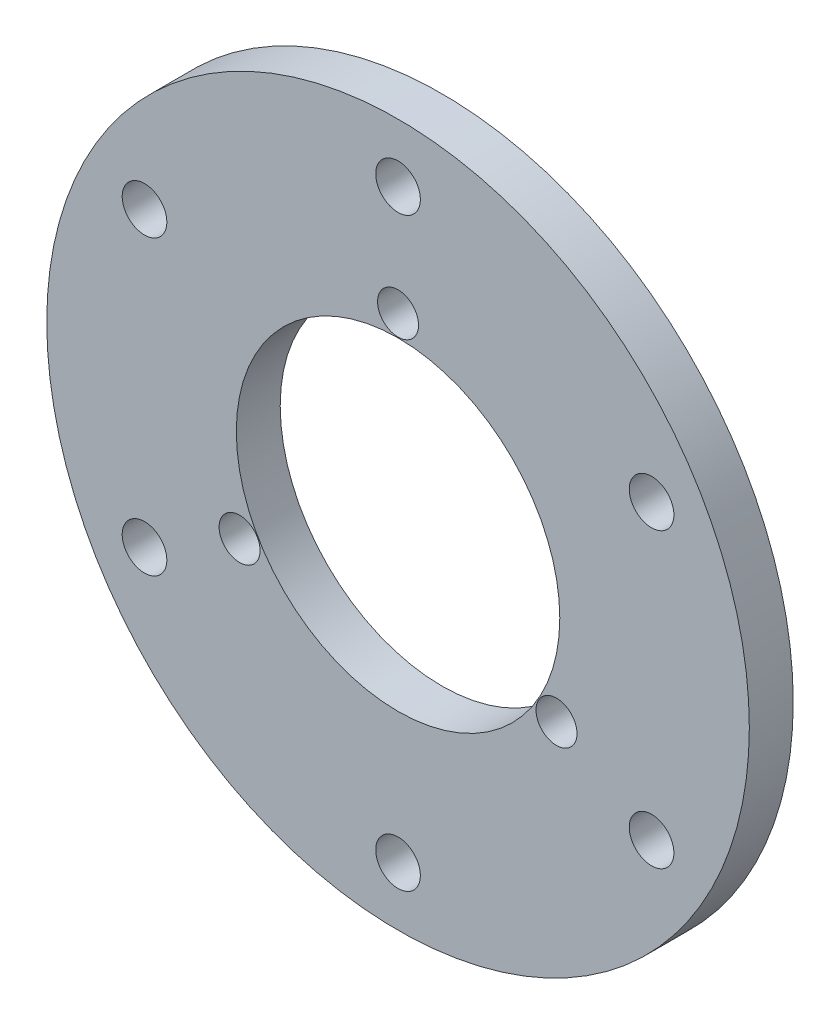
SolidWorks part; units mm, degrees
material "Thornel Mat VMA"
ref_plane "前视基准面" through (0, 0, 0) normal (0, 0, 1) x (1, 0, 0)
ref_plane "上视基准面" through (0, 0, 0) normal (0, 1, 0) x (1, 0, 0)
ref_plane "右视基准面" through (0, 0, 0) normal (1, 0, 0) x (0, 0, -1)
sketch "草图1" plane through (0, 0, 0) normal (0, 0, 1) x (1, 0, 0)
  circle A0 centre (0, 0) radius 11.05
  circle A1 centre (0, 0) radius 12.5 construction
  circle A2 centre (0, 0) radius 20 construction
  circle A3 centre (0, 0) radius 24
  circle A4 centre (0, 20) radius 1.525
  circle A5 centre (17.3205, 10) radius 1.525
  circle A6 centre (17.3205, -10) radius 1.525
  circle A7 centre (0, -20) radius 1.525
  circle A8 centre (-17.3205, -10) radius 1.525
  circle A9 centre (-17.3205, 10) radius 1.525
  circle A10 centre (0, 12.5) radius 1.4
  circle A11 centre (10.8253, -6.25) radius 1.4
  circle A12 centre (-10.8253, -6.25) radius 1.4
  point P20 (0, 0)
  point P27 (0, 0)
  dimension "D1" = 22.1
  dimension "D2" = 25
  dimension "D3" = 40
  dimension "D4" = 48
  dimension "D5" = 3.05
  dimension "D7" = 2.8
  dimension "D6" = 6
  dimension "D8" = 3
extrude "凸台-拉伸1" add sketch "草图1" along normal blind 3
